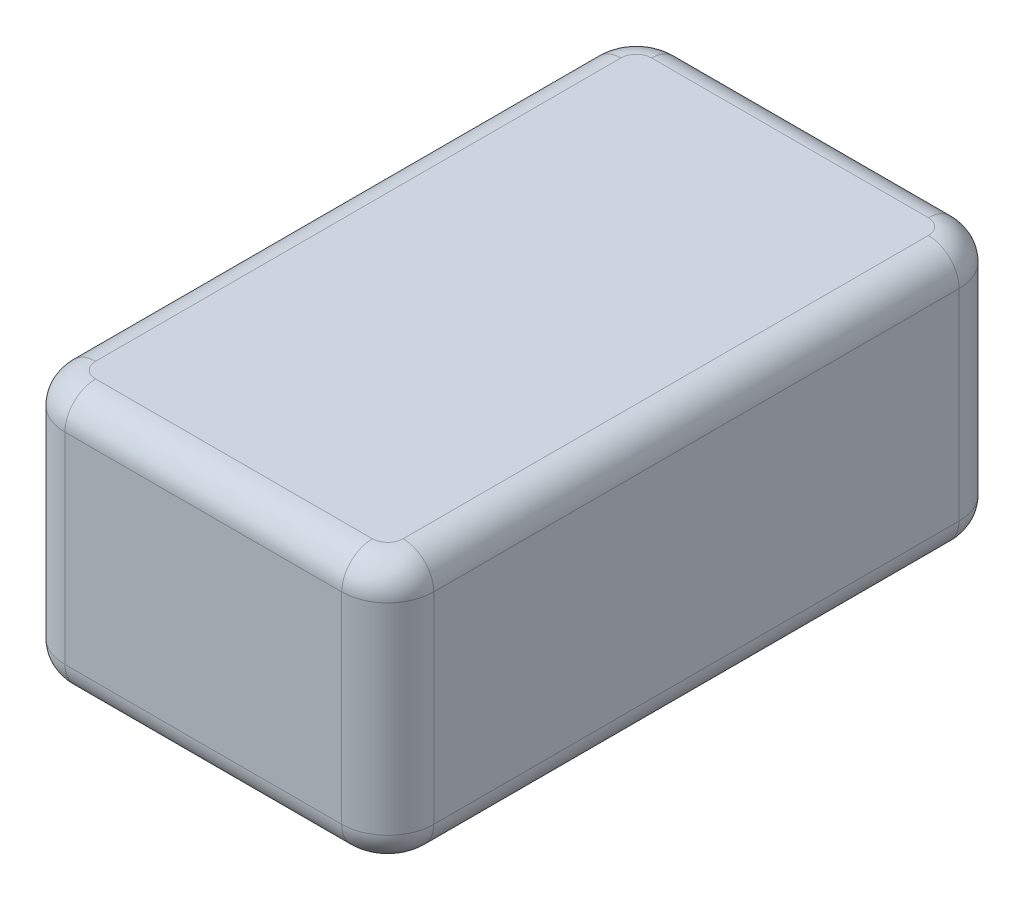
SolidWorks part; units mm, degrees
ref_plane "Front Plane" through (0, 0, 0) normal (0, 0, 1) x (1, 0, 0)
ref_plane "Top Plane" through (0, 0, 0) normal (0, 1, 0) x (1, 0, 0)
ref_plane "Right Plane" through (0, 0, 0) normal (1, 0, 0) x (0, 0, -1)
sketch "Sketch1" plane through (0, 0, 0) normal (0, 1, 0) x (1, 0, 0)
  line L1 (0, 0) -> (305.308, 0)
  line L2 (0, 0) -> (0, 511.048)
  line L3 (0, 511.048) -> (305.308, 511.048)
  line L4 (305.308, 0) -> (305.308, 511.048)
  dimension "D1" = 511.048
  dimension "D2" = 305.308
extrude "Boss-Extrude1" add sketch "Sketch1" along normal blind 217.424
fillet "Fillet1" radius 38.1 4 edges at (305.308, 108.712, -511.048) (0, 108.712, -511.048) (305.308, 108.712, 0) (0, 108.712, 0)
fillet "Fillet2" radius 25.4 16 edges at (294.1488, 0, -499.8888) (305.308, 0, -255.524) (294.1488, 0, -11.1592) (152.654, 0, 0) (11.1592, 0, -11.1592) (0, 0, -255.524) (11.1592, 0, -499.8888) (294.1488, 217.424, -499.8888) (305.308, 217.424, -255.524) (294.1488, 217.424, -11.1592) (152.654, 217.424, 0) (11.1592, 217.424, -11.1592) (0, 217.424, -255.524) (11.1592, 217.424, -499.8888) (152.654, 0, -511.048) (152.654, 217.424, -511.048)
